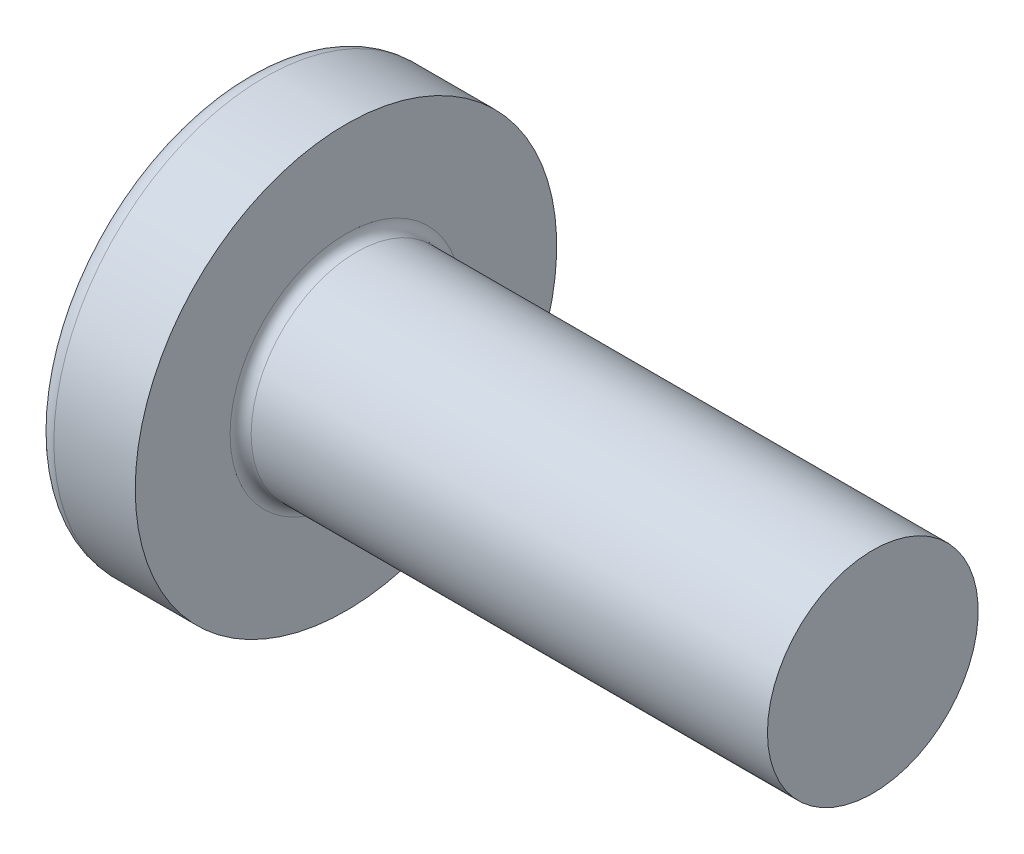
SolidWorks part; units mm, degrees
material "普通碳钢"
ref_plane "Plane1" through (0, 0, 0) normal (0, 0, 1) x (1, 0, 0)
ref_plane "Plane2" through (0, 0, 0) normal (0, 1, 0) x (1, 0, 0)
ref_plane "Plane3" through (0, 0, 0) normal (1, 0, 0) x (0, 0, -1)
sketch "BodySke" plane through (0, 0, 0) normal (0, 0, 1) x (1, 0, 0)
  line L0 (3.1, 2) -> (3.1, 4)
  line L1 (3.45, 6.35) -> (3.45, -3.175) construction
  line L2 (-25.4, 0) -> (127, 0) construction
  line L3 (13.1, 0) -> (0, 0)
  line L4 (3.1, 2) -> (13.1, 2)
  line L5 (13.1, 2) -> (13.1, 0)
  line L6 (1.5553, 4) -> (3.1, 4)
  line L8 (7.1, 6.35) -> (7.1, -3.175) construction
  arc A0 (1.2654, 3.8534) -> (0, 0) centre (6.5, 0) ccw
  arc A2 (1.2654, 3.8534) -> (1.5553, 4) centre (1.5553, 3.64) cw
  dimension "Head_fillet_rad" = 0.36
  dimension "Head_crown_rad" = 6.5
  dimension "Head_ht" = 3.1
  dimension "Diameter" = 4
  dimension "Length" = 10
  dimension "Head_dia" = 8
  dimension "Advance" = 0.7
  dimension "Thread_nom" = 6
revolve "Base-Revolve" add sketch "BodySke"
cosmetic thread "ThreadCosmetic" [suppressed]
fillet "Fillet1" radius 0.2 1 edges at (3.1, 0, 2)
sketch "Sketch3" plane through (0, 0, 0) normal (1, 0, 0) x (0, 0, -1)
  line L0 (0.515, -2.15) -> (-0.515, -2.15)
  line L1 (0.515, -2.15) -> (0.515, 2.15)
  line L2 (-0.515, 2.15) -> (0.515, 2.15)
  line L3 (-0.515, 2.15) -> (-0.515, -2.15)
  dimension "D1" = 2.15
  dimension "Cross_dia" = 4.3
  dimension "D2" = 0.515
  dimension "Cross_width" = 1.03
ref_plane "Plane4" through (2.34, 0, 0) normal (1, 0, 0) x (0, 0, -1)
sketch "Sketch4" plane through (2.34, 0, 0) normal (1, 0, 0) x (0, 0, -1)
  line L0 (0.515, -0.9833) -> (-0.515, -0.9833)
  line L1 (0.515, -0.9833) -> (0.515, 0.9833)
  line L2 (-0.515, 0.9833) -> (0.515, 0.9833)
  line L3 (-0.515, 0.9833) -> (-0.515, -0.9833)
  dimension "D1" = 1.03
  dimension "D2" = 1.9666
  dimension "D3" = 0.515
  dimension "D4" = 0.9833
loft "Recess" cut profiles "Sketch3", "Sketch4"
pattern_circular "RecPat" count 2 every 90 about axis through (0, 0, 0) along (1, 0, 0) of "Recess"
sketch "RecCorSke" plane through (0, 0, 0) normal (0, 0, 1) x (1, 0, 0)
  line L0 (-3.175, 0) -> (15.875, 0) construction
  line L1 (-25.4, 0) -> (127, 0) construction
  line L2 (0, 0) -> (0, 1.0146)
  line L3 (0, 1.0146) -> (2.34, 0.851)
  line L4 (2.34, 0.851) -> (2.6165, 0)
  line L5 (2.6165, 0) -> (0, 0)
  dimension "Diameter" = 1.702
  dimension "Depth" = 2.34
  dimension "Draft_angle" = 4
  dimension "Bottom_angle" = 18
revolve "RecessCore" cut sketch "RecCorSke" angle 360 about L0
sketch "ThdSchSke" plane through (0, 0, 0) normal (0, 0, 1) x (1, 0, 0)
  line L0 (7.1, -1.61) -> (6.8269, -2)
  line L1 (7.1, -1.61) -> (7.3731, -2)
  line L2 (7.3731, -2) -> (7.3731, -2.5)
  line L3 (-3.175, 0) -> (5.1513, 0) construction
  line L5 (7.3731, -2.5) -> (6.8269, -2.5)
  line L6 (6.8269, -2.5) -> (6.8269, -2)
  dimension "Thread_minor" = 3.22
  dimension "Diameter" = 4
  dimension "Start" = 7.1
  dimension "SideAngle" = 55
  dimension "VeeAngle" = 70
  dimension "Overcut" = 5
revolve "ThreadSchematic" [suppressed] cut sketch "ThdSchSke" angle 360 about L3
pattern_linear "ThdSchPat" [suppressed]
sketch "草图1" plane through (13.1, 0, 0) normal (1, 0, 0) x (0, 0, -1)
  circle A0 centre (0, 0) radius 2 construction
  circle A1 centre (0, 0) radius 2
equation "\"D1@Sketch3\" = \"Cross_dia@Sketch3\" / 2"
equation "\"D2@Sketch3\" = \"Cross_width@Sketch3\" / 2"
equation "\"Depth@RecCorSke\" = \"Cross_depth@Plane4\""
equation "\"D1@Sketch4\" = \"Cross_width@Sketch3\""
equation "\"D2@Sketch4\" = \"Cross_dia@Sketch3\" - 2.0 * \"Cross_depth@Plane4\" * tan(26.5  * 0.017453292)"
equation "\"D3@Sketch4\" = \"D1@Sketch4\" / 2"
equation "\"D4@Sketch4\" = \"D2@Sketch4\" / 2"
equation "\"Thread_length@ThreadCosmetic\" = ((sgn( (\"Length@BodySke\" - \"Advance@BodySke\" * 2.0 ) - \"Thread_nom@BodySke\" )-1)*( (\"Length@BodySke\" - \"Advance@BodySke\" * 2.0 ) - \"Thread_nom@BodySke\" ))/-2+ \"Thread_nom@BodySke\""
equation "\"Thread_minor@ThdSchSke\" = \"Thread_minor@ThreadCosmetic\""
equation "\"Diameter@ThdSchSke\" = \"Diameter@BodySke\""
equation "\"Overcut@ThdSchSke\" = \"Diameter@BodySke\" * 1.25"
equation "\"Start@ThdSchSke\" = \"Head_ht@BodySke\" + \"Length@BodySke\" - \"Thread_length@ThreadCosmetic\"  '---Non-countersunk---"
equation "\"Num_threads@ThdSchPat\" = int( \"Thread_length@ThreadCosmetic\" / \"Advance@BodySke\" + 0.999 )  + 1"
equation "\"Advance@ThdSchPat\" = \"Thread_length@ThreadCosmetic\" /  (\"Num_threads@ThdSchPat\" - 1) 'relax it"
